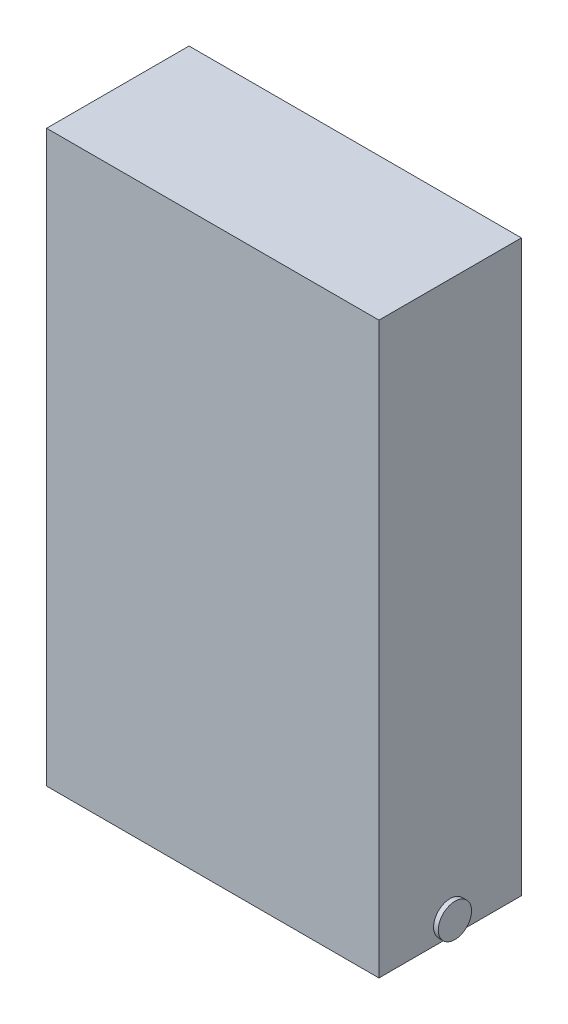
SolidWorks part; units mm, degrees
material "ABS"
ref_plane "Płaszczyzna przednia" through (0, 0, 0) normal (0, 0, 1) x (1, 0, 0)
ref_plane "Płaszczyzna górna" through (0, 0, 0) normal (0, 1, 0) x (1, 0, 0)
ref_plane "Płaszczyzna prawa" through (0, 0, 0) normal (1, 0, 0) x (0, 0, -1)
sketch "Szkic1" plane through (0, 0, 0) normal (0, 0, 1) x (1, 0, 0)
  line L1 (0, 0) -> (350, 0)
  line L2 (0, 0) -> (0, 600)
  line L3 (0, 600) -> (350, 600)
  line L4 (350, 0) -> (350, 600)
  dimension "D1" = 600
  dimension "D2" = 350
extrude "Dodanie-wyciągnięcie1" add sketch "Szkic1" along normal blind 150
sketch "Szkic2" plane through (0, 0, 0) normal (0, 0, -1) x (-1, 0, 0)
  line L0 (0, 0) -> (-350, 0) construction
  line L1 (-25, 25) -> (-325, 25)
  line L2 (-25, 25) -> (-25, 275)
  line L3 (-25, 275) -> (-325, 275)
  line L4 (-325, 25) -> (-325, 275)
  line L5 (0, 600) -> (0, 0) construction
  line L6 (-350, 0) -> (-350, 600) construction
  dimension "D1" = 25
  dimension "D2" = 25
  dimension "D3" = 25
  dimension "D4" = 250
extrude "Wytnij-wyciągnięcie1" cut sketch "Szkic2" against normal blind 100 from offset 2.5 offset against normal yes
sketch "Szkic3" plane through (350, 0, 0) normal (1, 0, 0) x (0, 0, -1)
  line L0 (0, 0) -> (0, 600) construction
  line L2 (-150, 0) -> (0, 0) construction
  circle A1 centre (-75, 17.5) radius 17.5
  dimension "D1" = 75
  dimension "D2" = 35
extrude "Dodanie-wyciągnięcie2" add sketch "Szkic3" along normal blind 5
ref_plane "Płaszczyzna2" through (175, 0, 0) normal (-1, 0, 0) x (0, 0, 1)
mirror "Lustro1" about plane through (175, 0, 0) normal (-1, 0, 0) of "Dodanie-wyciągnięcie2"
